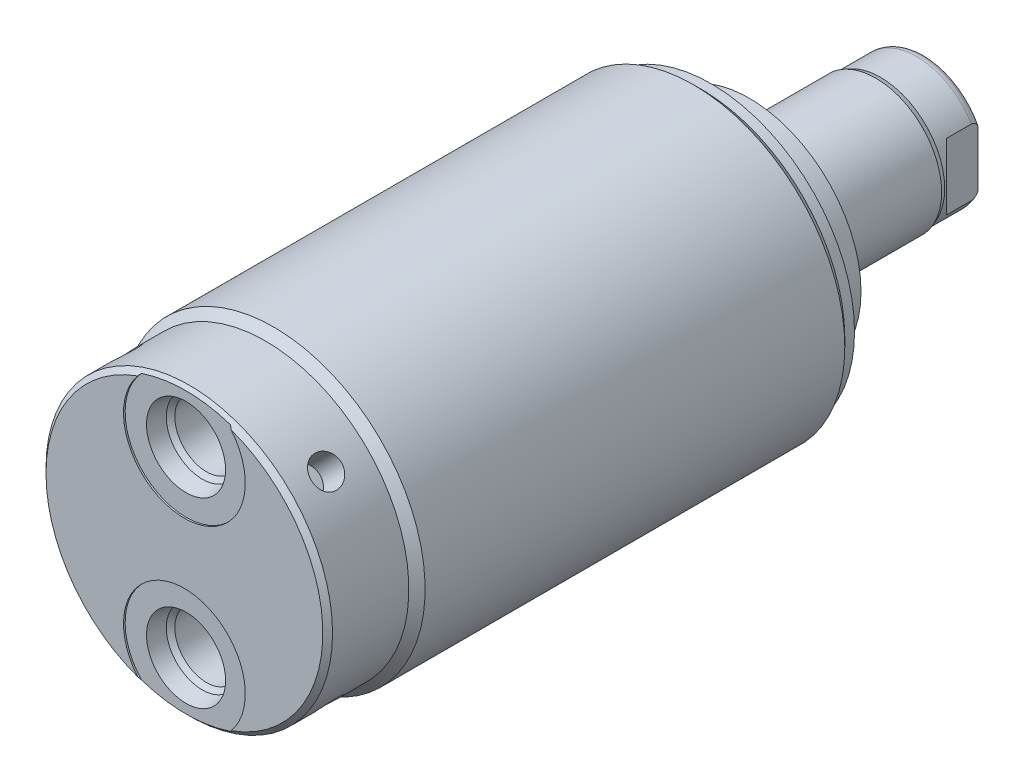
SolidWorks part; units mm, degrees
material "Alloy Steel"
ref_plane "Front Plane" through (0, 0, 0) normal (0, 0, 1) x (1, 0, 0)
ref_plane "Top Plane" through (0, 0, 0) normal (0, 1, 0) x (1, 0, 0)
ref_plane "Right Plane" through (0, 0, 0) normal (1, 0, 0) x (0, 0, -1)
ref_plane "Plane1" through (0, 0, 0) normal (0, 0, 1) x (1, 0, 0)
sketch "Sketch1" plane through (0, 0, 0) normal (0, 0, 1) x (1, 0, 0)
  circle A0 centre (0, 0) radius 23.6855
  dimension "D1" = 47.371
extrude "Extrude1" add sketch "Sketch1" along normal blind 82.423
sketch "Sketch2" plane through (0, 0, 0) normal (0, 1, 0) x (1, 0, 0)
  line L0 (23.6855, -82.423) -> (23.6855, -68.453)
  line L1 (23.6855, -68.453) -> (22.4155, -69.723)
  line L2 (22.4155, -69.723) -> (22.4155, -82.423)
  line L3 (22.4155, -82.423) -> (23.6855, -82.423)
  line L4 (0, 0) -> (0, -24.4965) construction
  line L5 (-23.6855, -82.423) -> (23.6855, -82.423) construction
  line L6 (23.6855, -82.423) -> (23.6855, 0) construction
  dimension "D1" = 12.7
  dimension "D2" = 44.831
  dimension "D3" = 45
revolve "Cut-Revolve1" cut sketch "Sketch2" angle 360 about L4
sketch "Sketch3" plane through (0, 0, 0) normal (0, 1, 0) x (1, 0, 0)
  line L0 (22.4155, 0) -> (22.4155, -1.524)
  line L1 (22.4155, -1.524) -> (23.6855, -2.794)
  line L2 (23.6855, -2.794) -> (23.6855, 0)
  line L3 (23.6855, 0) -> (22.4155, 0)
  line L4 (0, 0) -> (0, 3.0455) construction
  line L5 (22.4155, -82.423) -> (22.4155, -69.723) construction
  line L6 (23.6855, 0) -> (-23.6855, 0) construction
  line L7 (23.6855, -68.453) -> (23.6855, 0) construction
  dimension "D1" = 45
  dimension "D2" = 1.524
revolve "Cut-Revolve2" cut sketch "Sketch3" angle 360 about L4
chamfer "Chamfer1" distance 0.762 angle 45 1 edges at (-22.4155, 0, 82.423)
sketch "S2D0002" plane through (0, 0, 0) normal (1, 0, 0) x (0, -1, 0)
  line L0 (20.4597, -82.169) -> (23.7998, -82.169)
  line L1 (20.4597, -82.169) -> (19.9171, -79.6163)
  line L2 (19.9171, -79.6163) -> (19.2532, -78.9524)
  line L3 (19.2532, -78.9524) -> (19.2532, -68.199)
  line L4 (19.2532, -68.199) -> (14.2748, -68.199)
  line L5 (14.2748, -68.199) -> (14.2748, -82.423)
  line L6 (14.2748, -14.6685) -> (14.2748, 0.6985) construction
  line L8 (23.7998, -82.169) -> (23.7998, -82.423)
  line L9 (-22.4155, -82.423) -> (22.4155, -82.423) construction
  line L10 (23.7998, -82.423) -> (14.2748, -82.423)
  dimension "D1" = 19.05
  dimension "D2" = 9.9568
  dimension "D3" = 0.254
  dimension "D4" = 12.3698
  dimension "D5" = 12
  dimension "D6" = 45
  dimension "D7" = 2.5527
  dimension "D8" = 13.97
  dimension "D9" = 14.2748
revolve "Cut-Revolve3" cut sketch "S2D0002" angle 360 about L6
sketch "Sketch6" plane through (0, 0, 0) normal (0, 0, -1) x (-1, 0, 0)
  circle A0 centre (0, 0) radius 17.4625
  circle A1 centre (0, 0) radius 23.6855 construction
  dimension "D1" = 34.925
extrude "Extrude2" add sketch "Sketch6" along normal blind 5.969
sketch "Sketch7" plane through (0, 0, 0) normal (1, 0, 0) x (0, 0, -1)
  line L0 (5.969, 0) -> (5.969, -10.3187)
  line L1 (5.969, -10.3187) -> (33.147, -10.3187)
  line L2 (33.147, -10.3187) -> (33.147, 0)
  line L3 (33.147, 0) -> (5.969, 0)
  line L4 (0, 0) -> (9.7123, 0) construction
  line L5 (5.969, -17.4625) -> (5.969, 17.4625) construction
  dimension "D1" = 20.6375
  dimension "D2" = 27.178
revolve "Revolve1" add sketch "Sketch7" angle 360 about L4
sketch "S2D0001" plane through (0, 0, 0) normal (0, 1, 0) x (1, 0, 0)
  line L0 (3.2639, 31.2113) -> (3.2639, 18.2118)
  line L1 (3.2639, 18.2118) -> (0, 18.2118)
  line L2 (4.3815, 33.147) -> (0, 33.147)
  line L3 (0, 33.147) -> (0, 18.2118)
  line L4 (3.2639, 31.2113) -> (4.3815, 33.147)
  line L5 (0, -31.3084) -> (0, 2.765) construction
  line L6 (10.3188, 33.147) -> (-10.3188, 33.147) construction
  dimension "D1" = 8.763
  dimension "D2" = 30
  dimension "D3" = 14.9352
  dimension "D4" = 6.5278
revolve "Cut-Revolve5" cut sketch "S2D0001" angle 360 about L5
ref_plane "Plane8" through (0, 0, 0) normal (1, 0, 0) x (0, -1, 0)
sketch "Sketch9" plane through (0, 0, 0) normal (1, 0, 0) x (0, -1, 0)
  line L0 (-10.3188, 25.7302) -> (-10.033, 26.4922)
  line L1 (-10.033, 26.4922) -> (-10.033, 32.131)
  line L2 (0, 12.6594) -> (0, 20.8178) construction
  line L3 (10.3187, 33.147) -> (-10.3188, 33.147) construction
  line L4 (-9.6449, 33.147) -> (-10.3188, 33.147)
  line L5 (-10.3188, 33.147) -> (-10.3188, 25.7302)
  arc A0 (-9.6449, 33.147) -> (-10.033, 32.131) centre (-8.509, 32.131) ccw
  dimension "D1" = 1.524
  dimension "D2" = 1.016
  dimension "D3" = 20.066
  dimension "D4" = 0.762
  dimension "D5" = 7.4168
revolve "Cut-Revolve6" cut sketch "Sketch9" angle 360 about L2
sketch "Sketch13" plane through (0, 0, 0) normal (0, 1, 0) x (1, 0, 0)
  line L0 (8.5852, 33.147) -> (8.5852, 28.194)
  line L1 (8.5852, 28.194) -> (10.033, 26.7462)
  line L2 (-8.5852, 33.147) -> (-8.5852, 28.194)
  line L3 (-8.5852, 28.194) -> (-10.033, 26.7462)
  line L4 (9.6449, 33.147) -> (-9.6449, 33.147) construction
  line L5 (0, 13.7262) -> (0, 20.767) construction
  line L6 (10.033, 26.7462) -> (10.033, 33.147)
  line L8 (8.5852, 33.147) -> (10.033, 33.147)
  line L9 (10.033, 26.4922) -> (10.033, 32.131) construction
  line L10 (-10.033, 26.7462) -> (-10.033, 33.147)
  line L11 (-8.5852, 33.147) -> (-10.033, 33.147)
  dimension "D1" = 17.1704
  dimension "D2" = 135
  dimension "D3" = 4.953
extrude "Cut-Extrude4" cut sketch "Sketch13" against normal mid plane 39.685
ref_plane "Plane13" through (0, 0, 0) normal (0.7071, 0.7071, 0) x (0, 0, -1)
hole_wizard "Hole1" positions "3DSketch2" profile "Sketch14" legacy
sketch3d "3DSketch2"
  point P0 (-15.8502, 15.8502, 76.073)
  dimension "D1" = 6.35
sketch "Sketch14" plane through (-15.8502, 15.8502, 76.073) normal (0, 0, 1) x (-0.7071, -0.7071, 0)
  line L0 (0, 0) -> (0, 4.7498)
  line L1 (0, 4.7498) -> (2.3749, 4.7498)
  line L2 (2.3749, 4.7498) -> (2.3749, 0)
  line L3 (2.3749, 0) -> (0, 0)
  line L4 (0, 110) -> (0, -10) construction
  dimension "Diameter" = 4.7498
  dimension "Depth" = 4.7498
pattern_circular "CirPattern1" count 4 over 360 about axis through (0, 0, 0) along (0, 0, 1) of "Hole1"
pattern_linear "LPattern1" count 2 spacing 28.5496 along (0, 1, 0) of "Cut-Revolve3"
